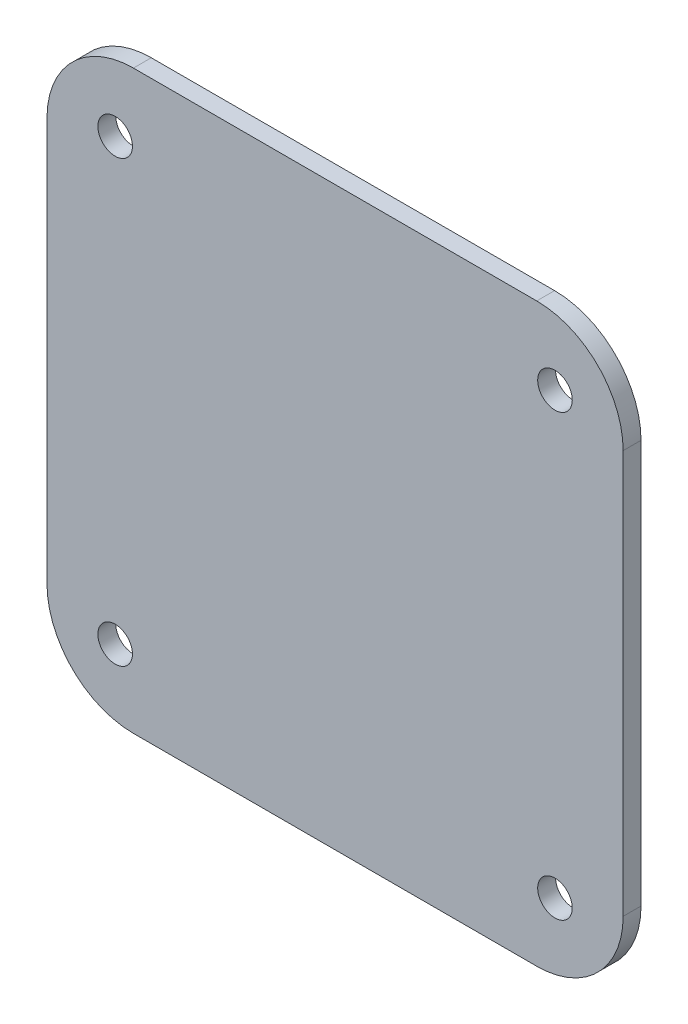
SolidWorks part; units mm, degrees
material "Teak"
ref_plane "Front Plane" through (0, 0, 0) normal (0, 0, 1) x (1, 0, 0)
ref_plane "Top Plane" through (0, 0, 0) normal (0, 1, 0) x (1, 0, 0)
ref_plane "Right Plane" through (0, 0, 0) normal (1, 0, 0) x (0, 0, -1)
sketch "Sketch1" plane through (0, 0, 0) normal (0, 0, 1) x (1, 0, 0)
  line L1 (-50, -50) -> (50, -50)
  line L2 (-50, -50) -> (-50, 50)
  line L3 (-50, 50) -> (50, 50)
  line L4 (50, -50) -> (50, 50)
  line L5 (-50, -50) -> (50, 50) construction
  line L6 (-50, 50) -> (50, -50) construction
  circle A0 centre (-38.1661, 38.1661) radius 3
  circle A2 centre (38.1661, 38.1661) radius 3
  circle A3 centre (38.1661, -38.1661) radius 3
  circle A4 centre (-38.1661, -38.1661) radius 3
  point P17 (0, 0)
  dimension "D5" = 107.95
  dimension "D2" = 6
  dimension "D6" = 0
  dimension "D8" = 100
  dimension "D3" = 90
  dimension "D4" = 4
  dimension "D1" = 100
  dimension "D7" = 0
extrude "Boss-Extrude2" add sketch "Sketch1" along normal blind 3.1
fillet "Fillet1" radius 15 4 edges at (-50, 50, 1.55) (-50, -50, 1.55) (50, -50, 1.55) (50, 50, 1.55)
equation "\"thick\" = 3.1mm"
equation "\"small_bearing_outer\"=12.9mm"
equation "\"servo1_L\"=40.7mm"
equation "\"servo1_W\"=20.5mm"
equation "\"servo1_H\"=43.5mm"
equation "\"servo1_hL\"=49mm"
equation "\"servo1_hW\"=10mm"
equation "\"servo1_H2\"=27mm"
equation "\"large_bearing_inner\"=2.75in"
equation "\"large_bearing_outer\"=4.75in"
equation "\"large_bearing_thick\"=3/8in"
equation "\"large_bearing_h1\"=3.25in"
equation "\"large_bearing_h2\"=4.25in"
equation "\"D5@Sketch1\"=\"large_bearing_h2\""
